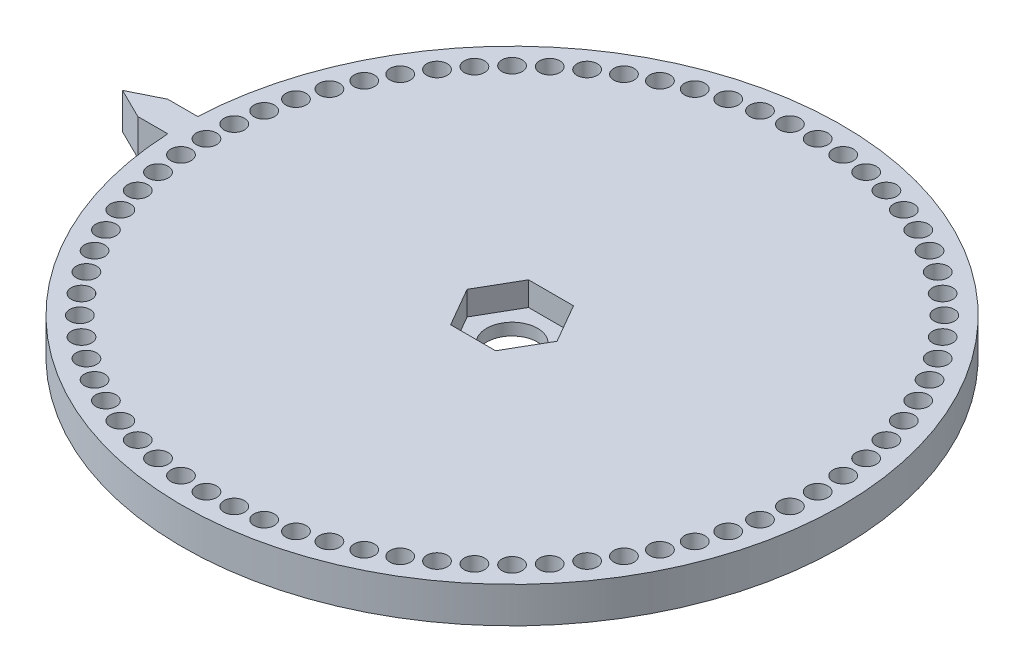
SolidWorks part; units mm, degrees
material "ABS PC"
ref_plane "Front Plane" through (0, 0, 0) normal (0, 0, 1) x (1, 0, 0)
ref_plane "Top Plane" through (0, 0, 0) normal (0, 1, 0) x (1, 0, 0)
ref_plane "Right Plane" through (0, 0, 0) normal (1, 0, 0) x (0, 0, -1)
sketch "Sketch1" plane through (0, 0, 0) normal (0, 1, 0) x (1, 0, 0)
  circle A0 centre (0, 0) radius 55
  dimension "D1" = 110
extrude "Boss-Extrude1" add sketch "Sketch1" along normal blind 6
sketch "Sketch2" plane through (0, 6, 0) normal (0, 1, 0) x (1, 0, 0)
  line L1 (3.7528, 6.5) -> (-3.7528, 6.5)
  line L2 (-3.7528, 6.5) -> (-7.5056, 0)
  line L3 (-7.5056, 0) -> (-3.7528, -6.5)
  line L4 (-3.7528, -6.5) -> (3.7528, -6.5)
  line L5 (3.7528, -6.5) -> (7.5056, 0)
  line L6 (7.5056, 0) -> (3.7528, 6.5)
  circle A0 centre (0, 0) radius 6.5 construction
  dimension "D1" = 13
extrude "Cut-Extrude1" cut sketch "Sketch2" against normal blind 4
sketch "Sketch3" plane through (0, 6, 0) normal (0, 1, 0) x (1, 0, 0)
  circle A0 centre (0, 51) radius 1.7
  point P51 (0, 0)
  dimension "D1" = 3.4
  dimension "D2" = 51
  dimension "D3" = 0
extrude "Cut-Extrude2" cut sketch "Sketch3" against normal through all
pattern_circular "CirPattern1" count 72 every 5 about axis through (0, 0, 0) along (0, 1, 0) of "Cut-Extrude2"
sketch "Sketch4" plane through (0, 2, 0) normal (0, 1, 0) x (1, 0, 0)
  circle A0 centre (0, 0) radius 4.25
  dimension "D1" = 8.5
extrude "Cut-Extrude3" cut sketch "Sketch4" against normal through all
sketch "Sketch5" plane through (0, 6, 0) normal (0, 1, 0) x (1, 0, 0)
  line L0 (-59.9432, 2.5) -> (-65, 0)
  line L1 (-54.9432, 2.5) -> (-54.9432, -2.5)
  line L2 (-65, 0) -> (-59.9432, -2.5)
  line L3 (-54.9432, 2.5) -> (-59.9432, 2.5)
  line L4 (3.7528, 6.5) -> (-3.7528, 6.5) construction
  line L7 (-54.9432, -2.5) -> (-59.9432, -2.5)
  circle A0 centre (0, 0) radius 4.25 construction
  circle A1 centre (0, 0) radius 55 construction
  dimension "D1" = 65
  dimension "D2" = 5
  dimension "D3" = 2.5
  dimension "D4" = 5
extrude "Boss-Extrude2" add sketch "Sketch5" against normal blind 6
